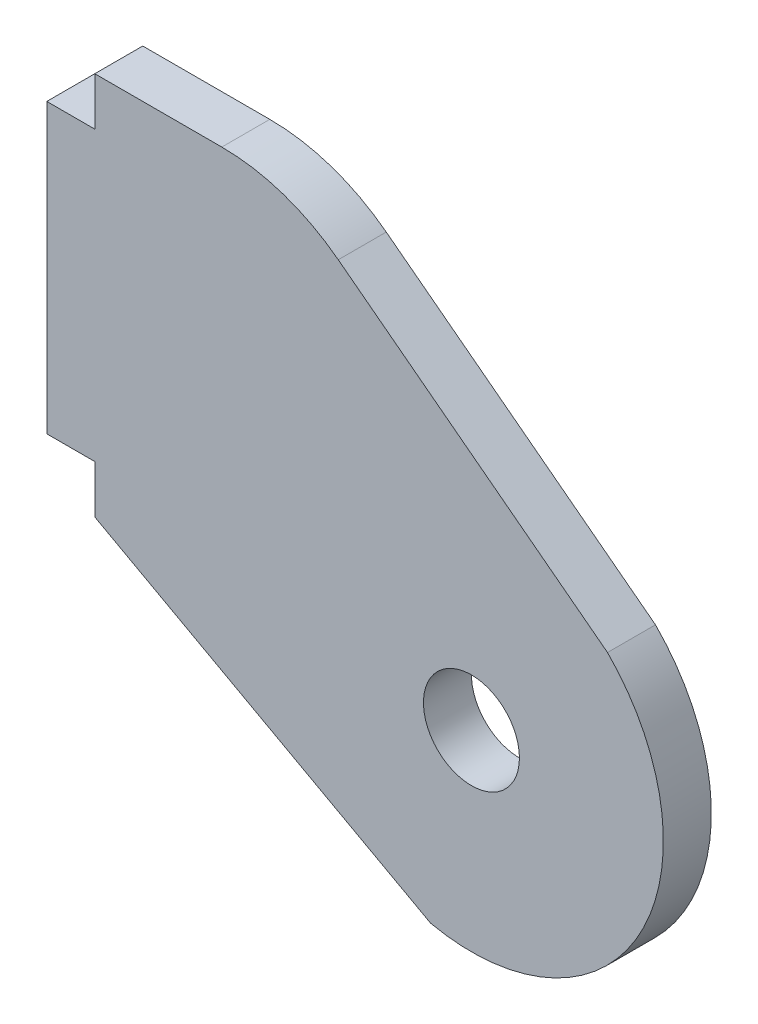
SolidWorks part; units mm, degrees
material "AISI 4340 Steel, annealed"
ref_plane "X-Y Datum" through (0, 0, 0) normal (0, 0, 1) x (1, 0, 0)
ref_plane "X-Z Datum" through (0, 0, 0) normal (0, 1, 0) x (1, 0, 0)
ref_plane "Y-Z Datum" through (0, 0, 0) normal (1, 0, 0) x (0, 0, -1)
sketch "Sketch1" plane through (0, 0, 0) normal (0, 0, 1) x (1, 0, 0)
  line L0 (427.9194, 0) -> (440.6194, 0)
  line L2 (427.9194, 0) -> (427.9194, -3.175)
  line L9 (427.9194, -25.4) -> (450.1444, -37.5712)
  line L10 (450.1444, -37.5712) -> (461.846, -16.2037) construction
  line L12 (440.6194, 0) -> (461.846, -16.2037)
  line L13 (427.9194, -22.225) -> (424.7444, -22.225)
  line L14 (424.7444, -22.225) -> (424.7444, -3.175)
  line L15 (424.7444, -3.175) -> (427.9194, -3.175)
  line L16 (427.9194, -22.225) -> (427.9194, -25.4)
  arc A0 (450.1444, -37.5712) -> (461.846, -16.2037) centre (452.8432, -25.1613) ccw
  dimension "D2" = 22.225
  dimension "D3" = 12.7
  dimension "D1" = 12.7
  dimension "D4" = 3.175
  dimension "D5" = 19.05
extrude "Boss-Extrude1" add sketch "Sketch1" along normal blind 3.175
hole_wizard "1/4 (0.25) Diameter Hole1" positions "Sketch2" profile "Sketch3" hole size "1/4" standard "ANSI Inch"
sketch "Sketch2" plane through (0, 0, 3.175) normal (0, 0, 1) x (1, 0, 0)
  point P0 (452.8432, -25.1613)
sketch "Sketch3" plane through (452.8432, -25.1613, 3.175) normal (1, 0, 0) x (0, -1, 0)
  line L0 (0, 0) -> (0, 11.176)
  line L1 (0, 11.176) -> (3.175, 9.2683)
  line L2 (3.175, 9.2683) -> (3.175, 0)
  line L5 (3.175, 0) -> (0, 0)
  line L10 (0, 11.176) -> (-3.175, 9.2683) construction
  line L11 (0, -6.35) -> (0, 107.95) construction
  dimension "Hole Dia." = 6.35
  dimension "Hole Depth" = 11.176
  dimension "Drill Angle" = 118
fillet "Fillet1" radius 12.7 1 edges at (440.6194, 0, 1.5875)
